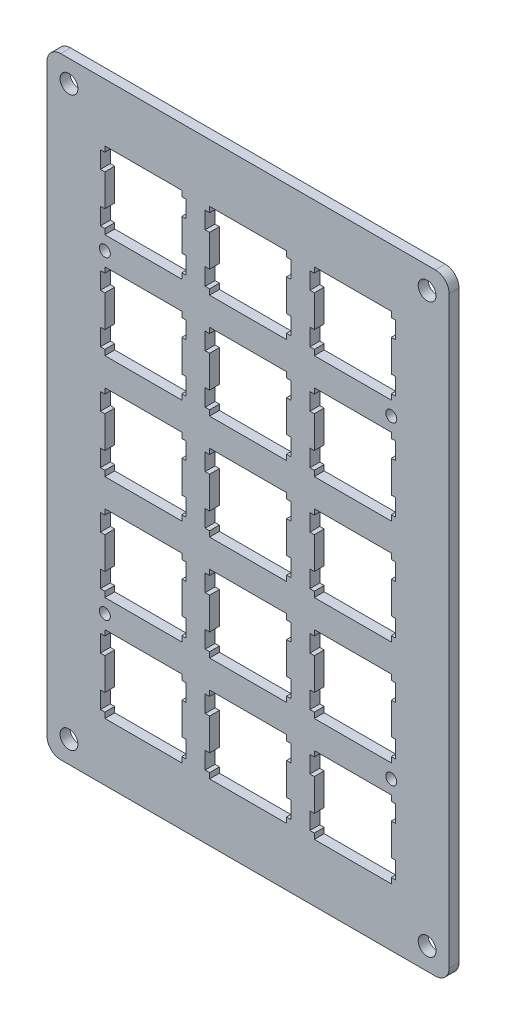
SolidWorks part; units mm, degrees
material "1023 碳钢板 (SS)"
ref_plane "前视基准面" through (0, 0, 0) normal (0, 0, 1) x (1, 0, 0)
ref_plane "上视基准面" through (0, 0, 0) normal (0, 1, 0) x (1, 0, 0)
ref_plane "右视基准面" through (0, 0, 0) normal (1, 0, 0) x (0, 0, -1)
sketch "Model" plane through (0, 0, 0) normal (0, 0, 1) x (1, 0, 0)
  line L0 (48.6251, 24.5257) -> (48.6251, 23.5253)
  line L1 (48.6251, 23.5253) -> (47.8243, 23.5253)
  line L2 (47.8243, 23.5253) -> (47.8243, 20.4274)
  line L3 (47.8243, 20.4274) -> (48.6251, 20.4274)
  line L4 (48.6251, 20.4274) -> (48.6251, 14.6259)
  line L5 (48.6251, 14.6259) -> (47.8243, 14.6259)
  line L6 (47.8243, 14.6259) -> (47.8243, 11.5253)
  line L7 (47.8243, 11.5253) -> (48.6251, 11.5253)
  line L8 (48.6251, 11.5253) -> (48.6251, 10.5262)
  line L9 (48.6251, 10.5262) -> (62.6244, 10.5262)
  line L10 (62.6244, 10.5262) -> (62.6244, 11.5253)
  line L11 (62.6244, 11.5253) -> (63.4252, 11.5253)
  line L12 (63.4252, 11.5253) -> (63.4252, 14.6259)
  line L13 (63.4252, 14.6259) -> (62.6244, 14.6259)
  line L14 (62.6244, 14.6259) -> (62.6244, 20.4274)
  line L15 (62.6244, 20.4274) -> (63.4252, 20.4274)
  line L16 (63.4252, 20.4274) -> (63.4252, 23.5253)
  line L17 (63.4252, 23.5253) -> (62.6244, 23.5253)
  line L18 (62.6244, 23.5253) -> (62.6244, 24.5257)
  line L19 (62.6244, 24.5257) -> (48.6251, 24.5257)
  line L20 (29.5751, 24.5257) -> (29.5751, 23.5253)
  line L21 (29.5751, 23.5253) -> (28.7744, 23.5253)
  line L22 (28.7744, 23.5253) -> (28.7744, 20.4274)
  line L23 (28.7744, 20.4274) -> (29.5751, 20.4274)
  line L24 (29.5751, 20.4274) -> (29.5751, 14.6259)
  line L25 (29.5751, 14.6259) -> (28.7744, 14.6259)
  line L26 (28.7744, 14.6259) -> (28.7744, 11.5253)
  line L27 (28.7744, 11.5253) -> (29.5751, 11.5253)
  line L28 (29.5751, 11.5253) -> (29.5751, 10.5262)
  line L29 (29.5751, 10.5262) -> (43.5744, 10.5262)
  line L30 (43.5744, 10.5262) -> (43.5744, 11.5253)
  line L31 (43.5744, 11.5253) -> (44.3752, 11.5253)
  line L32 (44.3752, 11.5253) -> (44.3752, 14.6259)
  line L33 (44.3752, 14.6259) -> (43.5744, 14.6259)
  line L34 (43.5744, 14.6259) -> (43.5744, 20.4274)
  line L35 (43.5744, 20.4274) -> (44.3752, 20.4274)
  line L36 (44.3752, 20.4274) -> (44.3752, 23.5253)
  line L37 (44.3752, 23.5253) -> (43.5744, 23.5253)
  line L38 (43.5744, 23.5253) -> (43.5744, 24.5257)
  line L39 (43.5744, 24.5257) -> (29.5751, 24.5257)
  line L40 (10.5251, 24.5257) -> (10.5251, 23.5253)
  line L41 (10.5251, 23.5253) -> (9.7244, 23.5253)
  line L42 (9.7244, 23.5253) -> (9.7244, 20.4274)
  line L43 (9.7244, 20.4274) -> (10.5251, 20.4274)
  line L44 (10.5251, 20.4274) -> (10.5251, 14.6259)
  line L45 (10.5251, 14.6259) -> (9.7244, 14.6259)
  line L46 (9.7244, 14.6259) -> (9.7244, 11.5253)
  line L47 (9.7244, 11.5253) -> (10.5251, 11.5253)
  line L48 (10.5251, 11.5253) -> (10.5251, 10.5262)
  line L49 (10.5251, 10.5262) -> (24.5246, 10.5262)
  line L50 (24.5246, 10.5262) -> (24.5246, 11.5253)
  line L51 (24.5246, 11.5253) -> (25.3252, 11.5253)
  line L52 (25.3252, 11.5253) -> (25.3252, 14.6259)
  line L53 (25.3252, 14.6259) -> (24.5246, 14.6259)
  line L54 (24.5246, 14.6259) -> (24.5246, 20.4274)
  line L55 (24.5246, 20.4274) -> (25.3252, 20.4274)
  line L56 (25.3252, 20.4274) -> (25.3252, 23.5253)
  line L57 (25.3252, 23.5253) -> (24.5246, 23.5253)
  line L58 (24.5246, 23.5253) -> (24.5246, 24.5257)
  line L59 (24.5246, 24.5257) -> (10.5251, 24.5257)
  line L60 (48.6251, 43.5756) -> (48.6251, 42.5753)
  line L61 (48.6251, 42.5753) -> (47.8243, 42.5753)
  line L62 (47.8243, 42.5753) -> (47.8243, 39.4774)
  line L63 (47.8243, 39.4774) -> (48.6251, 39.4774)
  line L64 (48.6251, 39.4774) -> (48.6251, 33.6759)
  line L65 (48.6251, 33.6759) -> (47.8243, 33.6759)
  line L66 (47.8243, 33.6759) -> (47.8243, 30.5753)
  line L67 (47.8243, 30.5753) -> (48.6251, 30.5753)
  line L68 (48.6251, 30.5753) -> (48.6251, 29.5762)
  line L69 (48.6251, 29.5762) -> (62.6244, 29.5762)
  line L70 (62.6244, 29.5762) -> (62.6244, 30.5753)
  line L71 (62.6244, 30.5753) -> (63.4252, 30.5753)
  line L72 (63.4252, 30.5753) -> (63.4252, 33.6759)
  line L73 (63.4252, 33.6759) -> (62.6244, 33.6759)
  line L74 (62.6244, 33.6759) -> (62.6244, 39.4774)
  line L75 (62.6244, 39.4774) -> (63.4252, 39.4774)
  line L76 (63.4252, 39.4774) -> (63.4252, 42.5753)
  line L77 (63.4252, 42.5753) -> (62.6244, 42.5753)
  line L78 (62.6244, 42.5753) -> (62.6244, 43.5756)
  line L79 (62.6244, 43.5756) -> (48.6251, 43.5756)
  line L80 (29.5751, 43.5756) -> (29.5751, 42.5753)
  line L81 (29.5751, 42.5753) -> (28.7744, 42.5753)
  line L82 (28.7744, 42.5753) -> (28.7744, 39.4774)
  line L83 (28.7744, 39.4774) -> (29.5751, 39.4774)
  line L84 (29.5751, 39.4774) -> (29.5751, 33.6759)
  line L85 (29.5751, 33.6759) -> (28.7744, 33.6759)
  line L86 (28.7744, 33.6759) -> (28.7744, 30.5753)
  line L87 (28.7744, 30.5753) -> (29.5751, 30.5753)
  line L88 (29.5751, 30.5753) -> (29.5751, 29.5762)
  line L89 (29.5751, 29.5762) -> (43.5744, 29.5762)
  line L90 (43.5744, 29.5762) -> (43.5744, 30.5753)
  line L91 (43.5744, 30.5753) -> (44.3752, 30.5753)
  line L92 (44.3752, 30.5753) -> (44.3752, 33.6759)
  line L93 (44.3752, 33.6759) -> (43.5744, 33.6759)
  line L94 (43.5744, 33.6759) -> (43.5744, 39.4774)
  line L95 (43.5744, 39.4774) -> (44.3752, 39.4774)
  line L96 (44.3752, 39.4774) -> (44.3752, 42.5753)
  line L97 (44.3752, 42.5753) -> (43.5744, 42.5753)
  line L98 (43.5744, 42.5753) -> (43.5744, 43.5756)
  line L99 (43.5744, 43.5756) -> (29.5751, 43.5756)
  line L100 (10.5251, 43.5756) -> (10.5251, 42.5753)
  line L101 (10.5251, 42.5753) -> (9.7244, 42.5753)
  line L102 (9.7244, 42.5753) -> (9.7244, 39.4774)
  line L103 (9.7244, 39.4774) -> (10.5251, 39.4774)
  line L104 (10.5251, 39.4774) -> (10.5251, 33.6759)
  line L105 (10.5251, 33.6759) -> (9.7244, 33.6759)
  line L106 (9.7244, 33.6759) -> (9.7244, 30.5753)
  line L107 (9.7244, 30.5753) -> (10.5251, 30.5753)
  line L108 (10.5251, 30.5753) -> (10.5251, 29.5762)
  line L109 (10.5251, 29.5762) -> (24.5246, 29.5762)
  line L110 (24.5246, 29.5762) -> (24.5246, 30.5753)
  line L111 (24.5246, 30.5753) -> (25.3252, 30.5753)
  line L112 (25.3252, 30.5753) -> (25.3252, 33.6759)
  line L113 (25.3252, 33.6759) -> (24.5246, 33.6759)
  line L114 (24.5246, 33.6759) -> (24.5246, 39.4774)
  line L115 (24.5246, 39.4774) -> (25.3252, 39.4774)
  line L116 (25.3252, 39.4774) -> (25.3252, 42.5753)
  line L117 (25.3252, 42.5753) -> (24.5246, 42.5753)
  line L118 (24.5246, 42.5753) -> (24.5246, 43.5756)
  line L119 (24.5246, 43.5756) -> (10.5251, 43.5756)
  line L120 (48.6251, 62.6257) -> (48.6251, 61.6252)
  line L121 (48.6251, 61.6252) -> (47.8243, 61.6252)
  line L122 (47.8243, 61.6252) -> (47.8243, 58.526)
  line L123 (47.8243, 58.526) -> (48.6251, 58.526)
  line L124 (48.6251, 58.526) -> (48.6251, 52.726)
  line L125 (48.6251, 52.726) -> (47.8243, 52.726)
  line L126 (47.8243, 52.726) -> (47.8243, 49.6254)
  line L127 (47.8243, 49.6254) -> (48.6251, 49.6254)
  line L128 (48.6251, 49.6254) -> (48.6251, 48.6264)
  line L129 (48.6251, 48.6264) -> (62.6244, 48.6264)
  line L130 (62.6244, 48.6264) -> (62.6244, 49.6254)
  line L131 (62.6244, 49.6254) -> (63.4252, 49.6254)
  line L132 (63.4252, 49.6254) -> (63.4252, 52.726)
  line L133 (63.4252, 52.726) -> (62.6244, 52.726)
  line L134 (62.6244, 52.726) -> (62.6244, 58.526)
  line L135 (62.6244, 58.526) -> (63.4252, 58.526)
  line L136 (63.4252, 58.526) -> (63.4252, 61.6252)
  line L137 (63.4252, 61.6252) -> (62.6244, 61.6252)
  line L138 (62.6244, 61.6252) -> (62.6244, 62.6257)
  line L139 (62.6244, 62.6257) -> (48.6251, 62.6257)
  line L140 (29.5751, 62.6257) -> (29.5751, 61.6252)
  line L141 (29.5751, 61.6252) -> (28.7744, 61.6252)
  line L142 (28.7744, 61.6252) -> (28.7744, 58.526)
  line L143 (28.7744, 58.526) -> (29.5751, 58.526)
  line L144 (29.5751, 58.526) -> (29.5751, 52.726)
  line L145 (29.5751, 52.726) -> (28.7744, 52.726)
  line L146 (28.7744, 52.726) -> (28.7744, 49.6254)
  line L147 (28.7744, 49.6254) -> (29.5751, 49.6254)
  line L148 (29.5751, 49.6254) -> (29.5751, 48.6264)
  line L149 (29.5751, 48.6264) -> (43.5744, 48.6264)
  line L150 (43.5744, 48.6264) -> (43.5744, 49.6254)
  line L151 (43.5744, 49.6254) -> (44.3752, 49.6254)
  line L152 (44.3752, 49.6254) -> (44.3752, 52.726)
  line L153 (44.3752, 52.726) -> (43.5744, 52.726)
  line L154 (43.5744, 52.726) -> (43.5744, 58.526)
  line L155 (43.5744, 58.526) -> (44.3752, 58.526)
  line L156 (44.3752, 58.526) -> (44.3752, 61.6252)
  line L157 (44.3752, 61.6252) -> (43.5744, 61.6252)
  line L158 (43.5744, 61.6252) -> (43.5744, 62.6257)
  line L159 (43.5744, 62.6257) -> (29.5751, 62.6257)
  line L160 (10.5251, 62.6257) -> (10.5251, 61.6252)
  line L161 (10.5251, 61.6252) -> (9.7244, 61.6252)
  line L162 (9.7244, 61.6252) -> (9.7244, 58.526)
  line L163 (9.7244, 58.526) -> (10.5251, 58.526)
  line L164 (10.5251, 58.526) -> (10.5251, 52.726)
  line L165 (10.5251, 52.726) -> (9.7244, 52.726)
  line L166 (9.7244, 52.726) -> (9.7244, 49.6254)
  line L167 (9.7244, 49.6254) -> (10.5251, 49.6254)
  line L168 (10.5251, 49.6254) -> (10.5251, 48.6264)
  line L169 (10.5251, 48.6264) -> (24.5246, 48.6264)
  line L170 (24.5246, 48.6264) -> (24.5246, 49.6254)
  line L171 (24.5246, 49.6254) -> (25.3252, 49.6254)
  line L172 (25.3252, 49.6254) -> (25.3252, 52.726)
  line L173 (25.3252, 52.726) -> (24.5246, 52.726)
  line L174 (24.5246, 52.726) -> (24.5246, 58.526)
  line L175 (24.5246, 58.526) -> (25.3252, 58.526)
  line L176 (25.3252, 58.526) -> (25.3252, 61.6252)
  line L177 (25.3252, 61.6252) -> (24.5246, 61.6252)
  line L178 (24.5246, 61.6252) -> (24.5246, 62.6257)
  line L179 (24.5246, 62.6257) -> (10.5251, 62.6257)
  line L180 (48.6251, 81.6757) -> (48.6251, 80.6752)
  line L181 (48.6251, 80.6752) -> (47.8243, 80.6752)
  line L182 (47.8243, 80.6752) -> (47.8243, 77.576)
  line L183 (47.8243, 77.576) -> (48.6251, 77.576)
  line L184 (48.6251, 77.576) -> (48.6251, 71.776)
  line L185 (48.6251, 71.776) -> (47.8243, 71.776)
  line L186 (47.8243, 71.776) -> (47.8243, 68.6754)
  line L187 (47.8243, 68.6754) -> (48.6251, 68.6754)
  line L188 (48.6251, 68.6754) -> (48.6251, 67.6764)
  line L189 (48.6251, 67.6764) -> (62.6244, 67.6764)
  line L190 (62.6244, 67.6764) -> (62.6244, 68.6754)
  line L191 (62.6244, 68.6754) -> (63.4252, 68.6754)
  line L192 (63.4252, 68.6754) -> (63.4252, 71.776)
  line L193 (63.4252, 71.776) -> (62.6244, 71.776)
  line L194 (62.6244, 71.776) -> (62.6244, 77.576)
  line L195 (62.6244, 77.576) -> (63.4252, 77.576)
  line L196 (63.4252, 77.576) -> (63.4252, 80.6752)
  line L197 (63.4252, 80.6752) -> (62.6244, 80.6752)
  line L198 (62.6244, 80.6752) -> (62.6244, 81.6757)
  line L199 (62.6244, 81.6757) -> (48.6251, 81.6757)
  line L200 (29.5751, 81.6757) -> (29.5751, 80.6752)
  line L201 (29.5751, 80.6752) -> (28.7744, 80.6752)
  line L202 (28.7744, 80.6752) -> (28.7744, 77.576)
  line L203 (28.7744, 77.576) -> (29.5751, 77.576)
  line L204 (29.5751, 77.576) -> (29.5751, 71.776)
  line L205 (29.5751, 71.776) -> (28.7744, 71.776)
  line L206 (28.7744, 71.776) -> (28.7744, 68.6754)
  line L207 (28.7744, 68.6754) -> (29.5751, 68.6754)
  line L208 (29.5751, 68.6754) -> (29.5751, 67.6764)
  line L209 (29.5751, 67.6764) -> (43.5744, 67.6764)
  line L210 (43.5744, 67.6764) -> (43.5744, 68.6754)
  line L211 (43.5744, 68.6754) -> (44.3752, 68.6754)
  line L212 (44.3752, 68.6754) -> (44.3752, 71.776)
  line L213 (44.3752, 71.776) -> (43.5744, 71.776)
  line L214 (43.5744, 71.776) -> (43.5744, 77.576)
  line L215 (43.5744, 77.576) -> (44.3752, 77.576)
  line L216 (44.3752, 77.576) -> (44.3752, 80.6752)
  line L217 (44.3752, 80.6752) -> (43.5744, 80.6752)
  line L218 (43.5744, 80.6752) -> (43.5744, 81.6757)
  line L219 (43.5744, 81.6757) -> (29.5751, 81.6757)
  line L220 (10.5251, 81.6757) -> (10.5251, 80.6752)
  line L221 (10.5251, 80.6752) -> (9.7244, 80.6752)
  line L222 (9.7244, 80.6752) -> (9.7244, 77.576)
  line L223 (9.7244, 77.576) -> (10.5251, 77.576)
  line L224 (10.5251, 77.576) -> (10.5251, 71.776)
  line L225 (10.5251, 71.776) -> (9.7244, 71.776)
  line L226 (9.7244, 71.776) -> (9.7244, 68.6754)
  line L227 (9.7244, 68.6754) -> (10.5251, 68.6754)
  line L228 (10.5251, 68.6754) -> (10.5251, 67.6764)
  line L229 (10.5251, 67.6764) -> (24.5246, 67.6764)
  line L230 (24.5246, 67.6764) -> (24.5246, 68.6754)
  line L231 (24.5246, 68.6754) -> (25.3252, 68.6754)
  line L232 (25.3252, 68.6754) -> (25.3252, 71.776)
  line L233 (25.3252, 71.776) -> (24.5246, 71.776)
  line L234 (24.5246, 71.776) -> (24.5246, 77.576)
  line L235 (24.5246, 77.576) -> (25.3252, 77.576)
  line L236 (25.3252, 77.576) -> (25.3252, 80.6752)
  line L237 (25.3252, 80.6752) -> (24.5246, 80.6752)
  line L238 (24.5246, 80.6752) -> (24.5246, 81.6757)
  line L239 (24.5246, 81.6757) -> (10.5251, 81.6757)
  line L240 (48.6251, 100.7257) -> (48.6251, 99.7252)
  line L241 (48.6251, 99.7252) -> (47.8243, 99.7252)
  line L242 (47.8243, 99.7252) -> (47.8243, 96.626)
  line L243 (47.8243, 96.626) -> (48.6251, 96.626)
  line L244 (48.6251, 96.626) -> (48.6251, 90.826)
  line L245 (48.6251, 90.826) -> (47.8243, 90.826)
  line L246 (47.8243, 90.826) -> (47.8243, 87.7254)
  line L247 (47.8243, 87.7254) -> (48.6251, 87.7254)
  line L248 (48.6251, 87.7254) -> (48.6251, 86.7264)
  line L249 (48.6251, 86.7264) -> (62.6244, 86.7264)
  line L250 (62.6244, 86.7264) -> (62.6244, 87.7254)
  line L251 (62.6244, 87.7254) -> (63.4252, 87.7254)
  line L252 (63.4252, 87.7254) -> (63.4252, 90.826)
  line L253 (63.4252, 90.826) -> (62.6244, 90.826)
  line L254 (62.6244, 90.826) -> (62.6244, 96.626)
  line L255 (62.6244, 96.626) -> (63.4252, 96.626)
  line L256 (63.4252, 96.626) -> (63.4252, 99.7252)
  line L257 (63.4252, 99.7252) -> (62.6244, 99.7252)
  line L258 (62.6244, 99.7252) -> (62.6244, 100.7257)
  line L259 (62.6244, 100.7257) -> (48.6251, 100.7257)
  line L260 (29.5751, 100.7257) -> (29.5751, 99.7252)
  line L261 (29.5751, 99.7252) -> (28.7744, 99.7252)
  line L262 (28.7744, 99.7252) -> (28.7744, 96.626)
  line L263 (28.7744, 96.626) -> (29.5751, 96.626)
  line L264 (29.5751, 96.626) -> (29.5751, 90.826)
  line L265 (29.5751, 90.826) -> (28.7744, 90.826)
  line L266 (28.7744, 90.826) -> (28.7744, 87.7254)
  line L267 (28.7744, 87.7254) -> (29.5751, 87.7254)
  line L268 (29.5751, 87.7254) -> (29.5751, 86.7264)
  line L269 (29.5751, 86.7264) -> (43.5744, 86.7264)
  line L270 (43.5744, 86.7264) -> (43.5744, 87.7254)
  line L271 (43.5744, 87.7254) -> (44.3752, 87.7254)
  line L272 (44.3752, 87.7254) -> (44.3752, 90.826)
  line L273 (44.3752, 90.826) -> (43.5744, 90.826)
  line L274 (43.5744, 90.826) -> (43.5744, 96.626)
  line L275 (43.5744, 96.626) -> (44.3752, 96.626)
  line L276 (44.3752, 96.626) -> (44.3752, 99.7252)
  line L277 (44.3752, 99.7252) -> (43.5744, 99.7252)
  line L278 (43.5744, 99.7252) -> (43.5744, 100.7257)
  line L279 (43.5744, 100.7257) -> (29.5751, 100.7257)
  line L280 (10.5251, 100.7257) -> (10.5251, 99.7252)
  line L281 (10.5251, 99.7252) -> (9.7244, 99.7252)
  line L282 (9.7244, 99.7252) -> (9.7244, 96.626)
  line L283 (9.7244, 96.626) -> (10.5251, 96.626)
  line L284 (10.5251, 96.626) -> (10.5251, 90.826)
  line L285 (10.5251, 90.826) -> (9.7244, 90.826)
  line L286 (9.7244, 90.826) -> (9.7244, 87.7254)
  line L287 (9.7244, 87.7254) -> (10.5251, 87.7254)
  line L288 (10.5251, 87.7254) -> (10.5251, 86.7264)
  line L289 (10.5251, 86.7264) -> (24.5246, 86.7264)
  line L290 (24.5246, 86.7264) -> (24.5246, 87.7254)
  line L291 (24.5246, 87.7254) -> (25.3252, 87.7254)
  line L292 (25.3252, 87.7254) -> (25.3252, 90.826)
  line L293 (25.3252, 90.826) -> (24.5246, 90.826)
  line L294 (24.5246, 90.826) -> (24.5246, 96.626)
  line L295 (24.5246, 96.626) -> (25.3252, 96.626)
  line L296 (25.3252, 96.626) -> (25.3252, 99.7252)
  line L297 (25.3252, 99.7252) -> (24.5246, 99.7252)
  line L298 (24.5246, 99.7252) -> (24.5246, 100.7257)
  line L299 (24.5246, 100.7257) -> (10.5251, 100.7257)
  line L300 (73.1507, 8.0003) -> (73.1507, 108.7501)
  line L301 (8.0005, 111.2501) -> (70.6507, 111.2501)
  line L302 (65.1507, 0.0003) -> (2.5005, 0.0003)
  line L303 (0.0005, 8.0003) -> (0.0005, 108.7501)
  line L304 (8.0005, 111.2501) -> (2.5005, 111.2501)
  line L305 (0.0005, 8.0003) -> (0.0005, 2.5003)
  line L306 (65.1507, 0.0003) -> (70.6507, 0.0003)
  line L307 (73.1507, 8.0003) -> (73.1507, 2.5003)
  line L308 (10.5251, 62.6257) -> (10.5251, 67.6764)
  arc A0 (0.0005, 2.5003) -> (2.5005, 0.0003) centre (2.5005, 2.5003) ccw
  arc A1 (70.6507, 0.0003) -> (73.1507, 2.5003) centre (70.6507, 2.5003) ccw
  arc A2 (73.1507, 108.7501) -> (70.6507, 111.2501) centre (70.6507, 108.7501) ccw
  arc A3 (2.5005, 111.2501) -> (0.0005, 108.7501) centre (2.5005, 108.7501) ccw
  circle A4 centre (10.5251, 27.0509) radius 1
  circle A5 centre (62.6244, 27.0509) radius 1
  circle A6 centre (10.5251, 84.201) radius 1
  circle A7 centre (62.6244, 84.201) radius 1
  circle A8 centre (69.1507, 107.2501) radius 1.625
  circle A9 centre (4.0005, 107.2501) radius 1.625
  circle A10 centre (4.0005, 4.0003) radius 1.625
  circle A11 centre (69.1507, 4.0003) radius 1.625
extrude "凸台-拉伸1" add sketch "Model" along normal blind 1.8 contours L304 A3 L303 L305 A0 L302 L306 A1 L307 L300 A2 L301 A11 A10 A9 A8 A7 A6 A5 A4 L19 L18 L17 L16 L15 L14 L13 L12 L11 L10 L9 L8 L7 L6 L5 L4 L3 L2 L1 L0 L39
